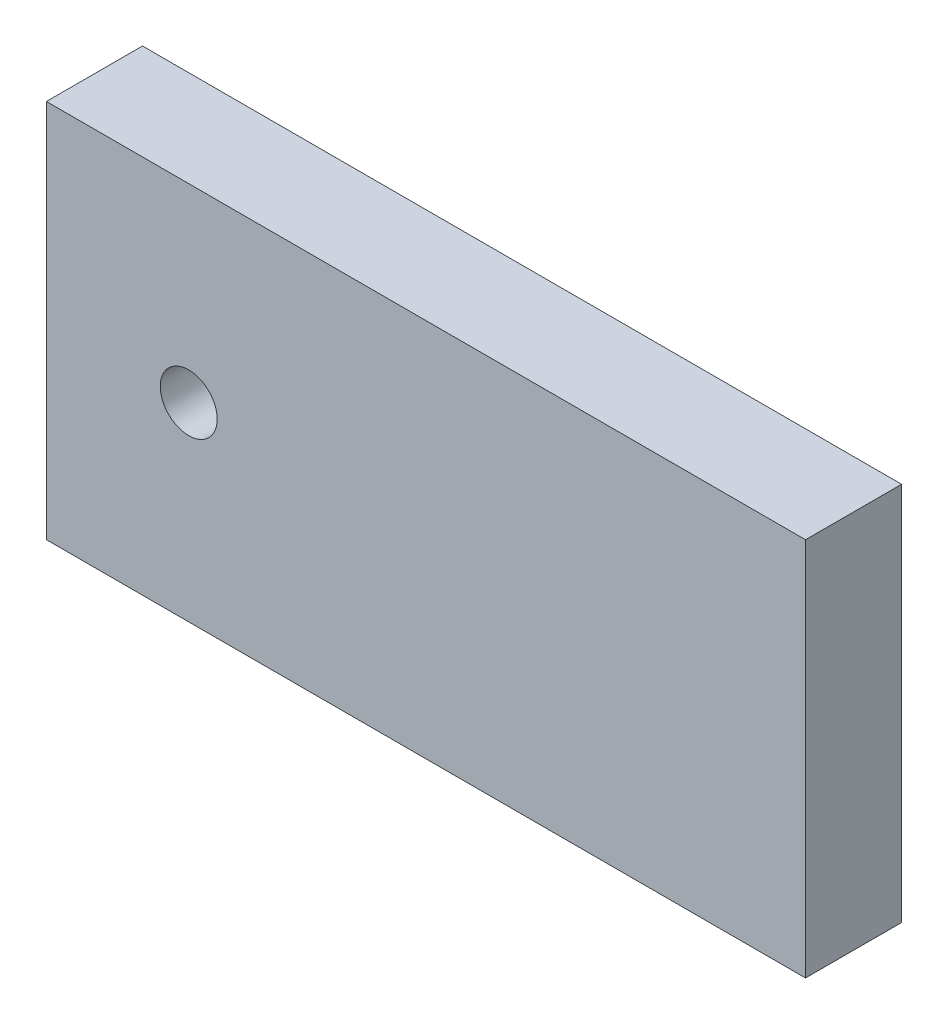
SolidWorks part; units mm, degrees
ref_plane "Plan de face" through (0, 0, 0) normal (0, 0, 1) x (1, 0, 0)
ref_plane "Plan de dessus" through (0, 0, 0) normal (0, 1, 0) x (1, 0, 0)
ref_plane "Plan de droite" through (0, 0, 0) normal (1, 0, 0) x (0, 0, -1)
sketch "Esquisse1" plane through (0, 0, 0) normal (0, 0, 1) x (1, 0, 0)
  line L1 (0, 0) -> (80, 0)
  line L2 (0, 0) -> (0, 40)
  line L3 (0, 40) -> (80, 40)
  line L4 (80, 0) -> (80, 40)
  dimension "D1" = 80
  dimension "D2" = 40
extrude "Boss.-Extru.2" add sketch "Esquisse1" along normal blind 10.125
sketch "Esquisse3" plane through (0, 0, 10.125) normal (0, 0, 1) x (1, 0, 0)
  line L0 (0, 40) -> (0, 0) construction
  line L1 (0, 0) -> (80, 0) construction
  circle A0 centre (15, 20) radius 3
  point P6 (-21.9769, 13.5458)
  dimension "D1" = 6
  dimension "D2" = 15
  dimension "D3" = 20
extrude "Enlèv. mat.-Extru.1" cut sketch "Esquisse3" against normal blind 10.125 contours A0
